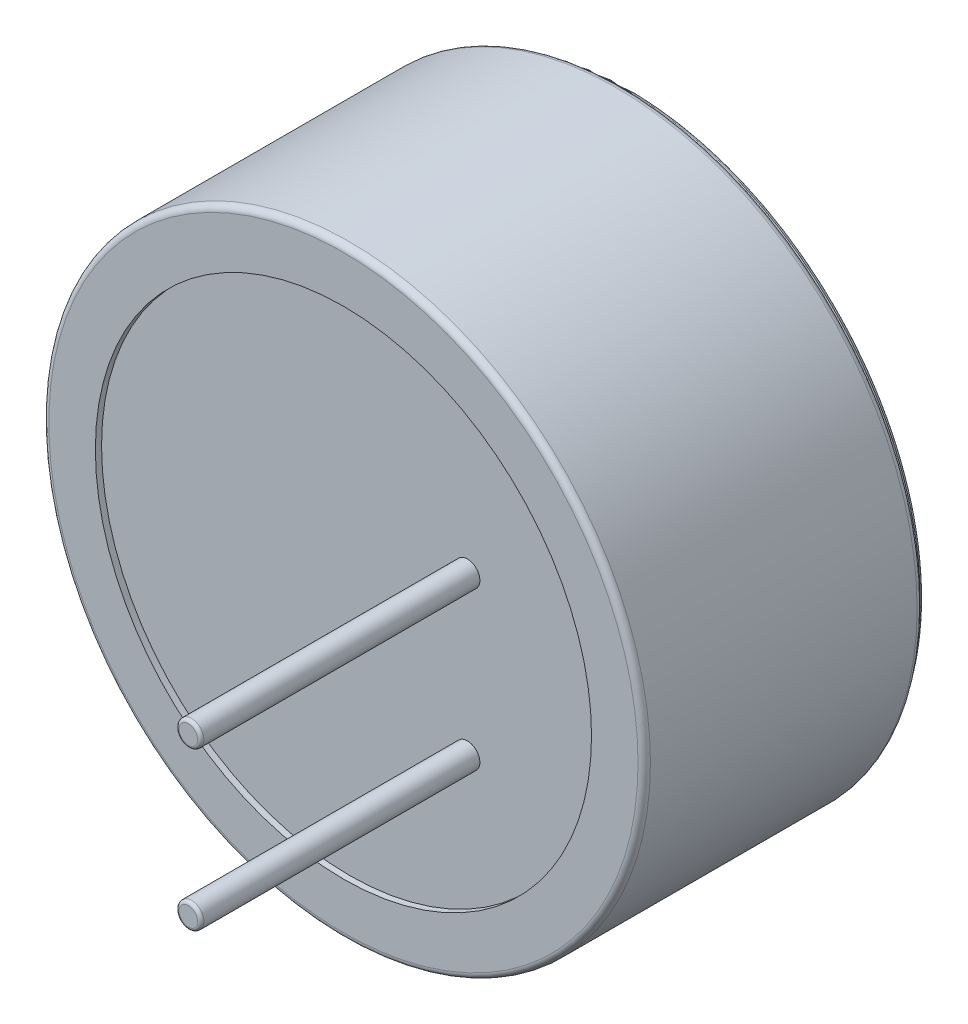
SolidWorks part; units mm, degrees
ref_plane "Front Plane" through (0, 0, 0) normal (0, 0, 1) x (1, 0, 0)
ref_plane "Top Plane" through (0, 0, 0) normal (0, 1, 0) x (1, 0, 0)
ref_plane "Right Plane" through (0, 0, 0) normal (1, 0, 0) x (0, 0, -1)
sketch "Sketch1" plane through (0, 0, 0) normal (0, 0, 1) x (1, 0, 0)
  circle A0 centre (0, 0) radius 4.85
extrude "Boss-Extrude1" add sketch "Sketch1" along normal blind 4.5
sketch "Sketch3" plane through (0, 0, 4.5) normal (0, 0, 1) x (1, 0, 0)
  circle A0 centre (2, -1.27) radius 0.2
  circle A1 centre (2, 1.27) radius 0.2
  dimension "D1" = 0.4
extrude "Boss-Extrude2" add sketch "Sketch3" along normal blind 4.5 separate body
fillet "Fillet1" radius 0.1 2 edges at (4.85, 0, 4.5) (4.85, 0, 0)
sketch "Sketch4" plane through (0, 0, 0) normal (0, 0, -1) x (-1, 0, 0)
  circle A0 centre (0, 0) radius 4.75
  circle A1 centre (0, 0) radius 4.75 construction
extrude "Boss-Extrude3" add sketch "Sketch4" along normal blind 0.1 separate body
fillet "Fillet2" radius 0.05 1 edges at (-4.75, 0, -0.1)
sketch "Sketch6" plane through (0, 0, 4.5) normal (0, 0, 1) x (1, 0, 0)
  circle A0 centre (0, 0) radius 4
extrude "Cut-Extrude1" cut sketch "Sketch6" against normal blind 0.1
fillet "Fillet3" radius 0.05 1 edges at (2.2, -1.27, 9)
fillet "Fillet4" radius 0.05 1 edges at (1.8, 1.27, 9)
